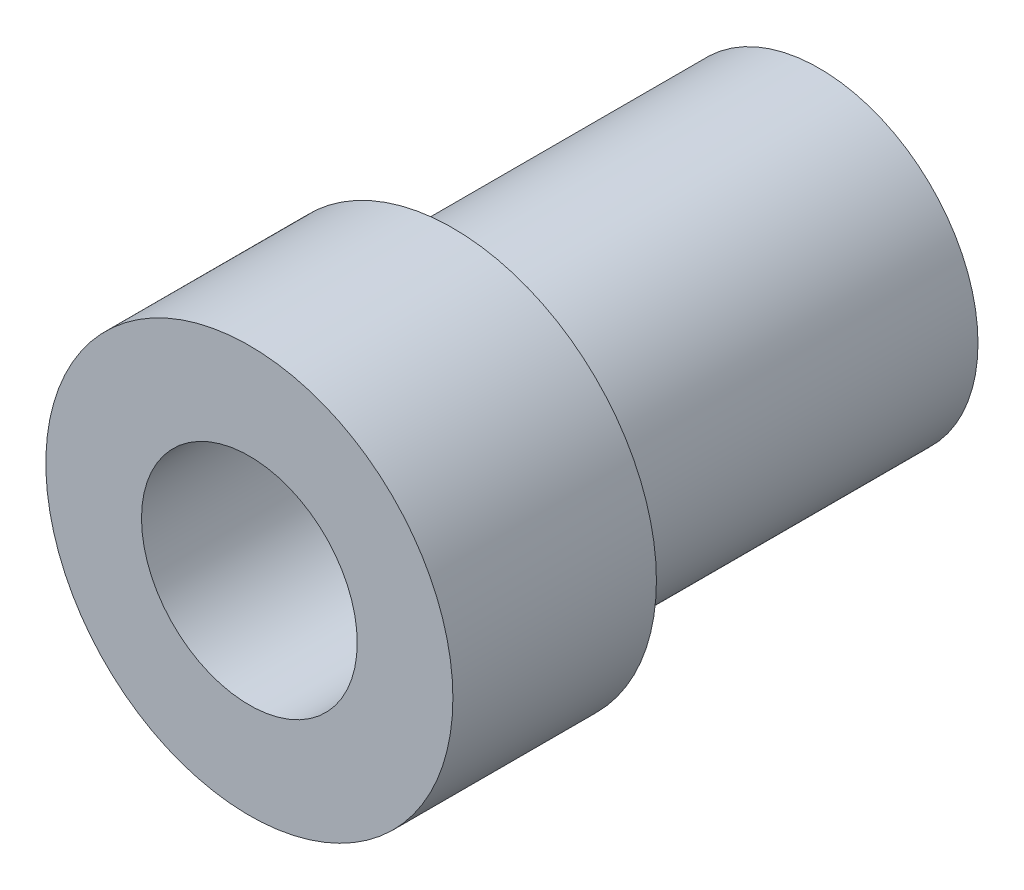
SolidWorks part; units mm, degrees
ref_plane "Piano frontale" through (0, 0, 0) normal (0, 0, 1) x (1, 0, 0)
ref_plane "Piano superiore" through (0, 0, 0) normal (0, 1, 0) x (1, 0, 0)
ref_plane "Piano destro" through (0, 0, 0) normal (1, 0, 0) x (0, 0, -1)
sketch "Schizzo1" plane through (0, 0, 0) normal (0, 0, 1) x (1, 0, 0)
  circle A0 centre (0, 0) radius 2.65
  circle A1 centre (0, 0) radius 3.9
  dimension "D1" = 5.3
  dimension "D2" = 7.8
extrude "Estrusione-Estrusione1" add sketch "Schizzo1" along normal blind 9
sketch "Schizzo2" plane through (0, 0, 9) normal (0, 0, 1) x (1, 0, 0)
  circle A0 centre (0, 0) radius 5
  circle A1 centre (0, 0) radius 3.9
  dimension "D1" = 10
  dimension "D2" = 7.8
extrude "Estrusione-Estrusione3" add sketch "Schizzo2" along normal blind 5 separate body
sketch "Schizzo3" plane through (0, 0, 9) normal (0, 0, 1) x (1, 0, 0)
  circle A0 centre (0, 0) radius 2.65
  circle A1 centre (0, 0) radius 3.9
  dimension "D1" = 5.3
  dimension "D2" = 7.8
extrude "Estrusione-Estrusione4" add sketch "Schizzo3" along normal up to surface (5 mm away) up to face at (5, 0, 14)
